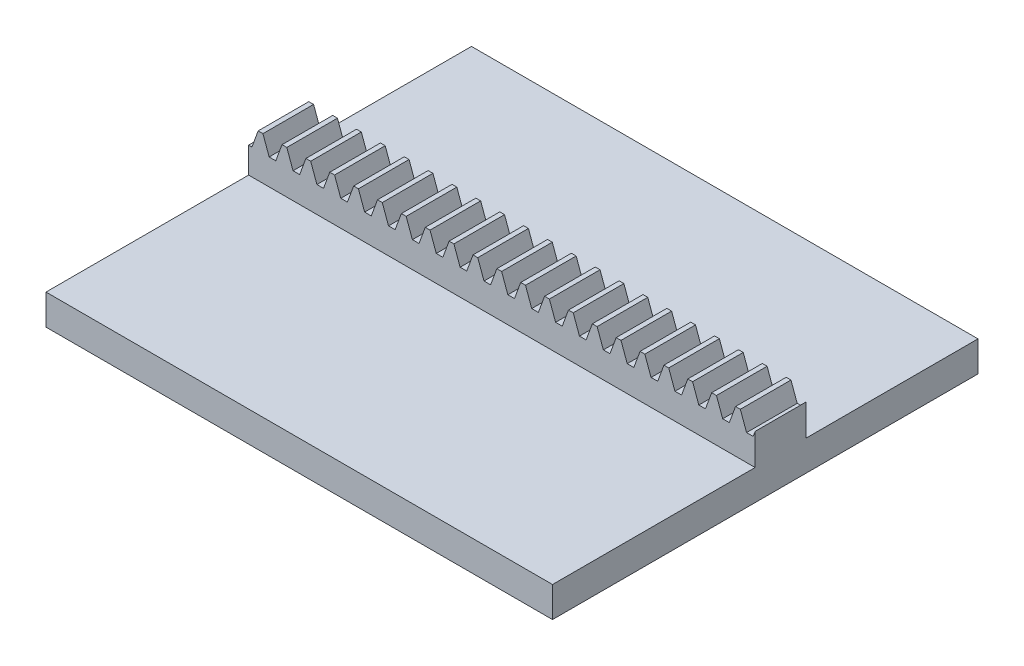
SolidWorks part; units mm, degrees
extrude "Blank" add sketch "BlankSke" against normal blind 10
sketch "BlankSke" plane through (0, 0, 0) normal (0, 0, 1) x (1, 0, 0)
  line L1 (0, 0) -> (100, 0)
  line L2 (0, 0) -> (0, 11.5)
  line L3 (0, 11.5) -> (100, 11.5)
  line L4 (100, 0) -> (100, 11.5)
  dimension "Length" = 100
  dimension "Blank_height" = 11.5
ref_plane "Plane1" through (0, 0, 0) normal (0, 0, 1) x (1, 0, 0)
ref_plane "Plane2" through (0, 0, 0) normal (0, 1, 0) x (1, 0, 0)
ref_plane "Plane3" through (0, 0, 0) normal (1, 0, 0) x (0, 0, -1)
other "Configuration Table"
sketch "HoldingSke" plane through (0, 0, 0) normal (0, 1, 0) x (1, 0, 0)
  line L0 (0, 0) -> (0.0928, 0.6602)
  line L1 (-15, 0) -> (100, 0) construction
  line L2 (0, 0) -> (-2.1039, 2.3779)
  line L3 (0, 0) -> (-11.863, 4.5341)
  line L4 (0, 0) -> (7.9495, 3.3743)
  line L5 (0, 0) -> (-23.7986, -8.8762)
  line L6 (0, 0) -> (-10.5278, -7.1032)
  line L9 (-71.009, 38.7566) -> (22.9603, 72.9586)
  line L10 (-76.2, 3.8779) -> (-66.2, 3.8779)
  line L11 (0, 0) -> (-10, 0)
  line L12 (-76.2, 101.6) -> (-76.147, 101.6)
  line L13 (24.9733, 27.94) -> (52.9518, 28.4284)
  line L14 (24.9733, 27.94) -> (24.9743, 27.94)
  line L15 (24.9733, 27.94) -> (100.4006, 29.5858)
  circle A0 centre (0, 0) radius 19.05
  circle A1 centre (0, 0) radius 5
  circle A2 centre (0, 0) radius 12.7
  dimension "MPH" = 10
  dimension "Diameter" = 38.1
  dimension "Num_teeth" = 23
  dimension "Pitch" = 0.6667
  dimension "Show_teeth" = 998
  dimension "Thickness" = 12.7
  dimension "Ap" = 20
  dimension "Pitch_height" = 10
  dimension "Width" = 10
  dimension "Backlash" = 0.053
  dimension "Addendum_fac" = 1
  dimension "Dedendum_fac" = 1.25
  dimension "Clearance_fac" = 0.25
  dimension "Dedendum_add" = 0.001
  dimension "Length" = 100
  dimension "Module" = 1.5
sketch "TooCutSkeIll" plane through (0, 0, 0) normal (0, 0, 1) x (1, 0, 0)
  line L0 (-1.8687, 11.4605) -> (-0.7447, 8.3724)
  line L1 (-0.3914, 8.125) -> (0.3914, 8.125)
  line L2 (0.7447, 8.3724) -> (1.8687, 11.4605)
  line L3 (100, 11.5) -> (0, 11.5) construction
  line L4 (0, 0) -> (0, 64.897) construction
  line L5 (-13.208, 10) -> (12.954, 10) construction
  line L6 (0, 0) -> (100, 0) construction
  line L7 (1.3371, 10) -> (1.3371, 48.7463) construction
  line L8 (-1.3371, 10) -> (-1.3371, 48.7463) construction
  line L9 (1.9251, 11.5) -> (1.9251, 11.5254)
  line L10 (-1.9251, 11.5) -> (-1.9251, 11.5254)
  line L11 (-1.9251, 11.5254) -> (1.9251, 11.5254)
  arc A0 (0.3914, 8.125) -> (0.7447, 8.3724) centre (0.3914, 8.501) ccw
  arc A1 (-0.7447, 8.3724) -> (-0.3914, 8.125) centre (-0.3914, 8.501) ccw
  arc A2 (1.9251, 11.5) -> (1.8687, 11.4605) centre (1.9251, 11.44) ccw
  arc A3 (-1.8687, 11.4605) -> (-1.9251, 11.5) centre (-1.9251, 11.44) ccw
  dimension "Pitch_height" = 10
  dimension "Addendum_plus" = 1.5254
  dimension "Pressure_angle" = 20
  dimension "Gap_width" = 2.6742
  dimension "Dedendum" = 1.875
extrude "ToothCutIll" [suppressed] cut sketch "TooCutSkeIll" against normal through all
sketch "TooCutSkeSim" plane through (0, 0, 0) normal (0, 0, 1) x (1, 0, 0)
  line L0 (0.6547, 8.125) -> (-0.6547, 8.125)
  line L1 (1.8923, 11.5254) -> (0.6547, 8.125)
  line L2 (0, 17.4625) -> (0, 53.467) construction
  line L3 (1.8923, 11.5254) -> (-1.8923, 11.5254)
  line L6 (-1.8923, 11.5254) -> (-0.6547, 8.125)
  line L9 (-1.3371, 10) -> (1.3371, 10) construction
  line L10 (0, 0) -> (100, 0) construction
  line L11 (1.3371, 10) -> (1.3371, 53.467) construction
  line L12 (-1.3371, 10) -> (-1.3371, 53.467) construction
  dimension "Pitch_height" = 10
  dimension "Addendum_plus" = 1.5254
  dimension "Pressure_angle" = 20
  dimension "Gap_width" = 2.6742
  dimension "Dedendum" = 1.875
extrude "ToothCutSim" cut sketch "TooCutSkeSim" against normal through all
pattern_linear "TeethCuts" count 22 spacing 4.7124 along (1, 0, 0) of "ToothCutIll", "ToothCutSim"
sketch "Sketch1" plane through (0, 0, 0) normal (0, 0, 1) x (1, 0, 0)
  line L4 (0, 8.125) -> (0, 0) construction
  line L5 (0, 3.044) -> (0, 0)
sketch "Sketch2" plane through (100, 0, 0) normal (1, 0, 0) x (0, 0, -1)
  line L25 (44.0001, 0) -> (44.0001, 3)
  line L26 (-40, 0) -> (44.0001, 0)
  line L27 (-40, 0) -> (-40, -3)
  line L28 (-40, -3) -> (44.0001, -3)
  line L29 (44.0001, 0) -> (44.0001, -3)
  line L30 (44.0001, 3) -> (10, 3)
  line L31 (10, 3) -> (10, 0)
  line L32 (10, 0) -> (44.0001, 0)
  line L33 (-40, 0) -> (0, 0)
  line L34 (0, 0) -> (0, 3)
  line L35 (0, 3) -> (-40, 3)
  line L36 (-40, 3) -> (-40, 0)
  line L37 (0, 0) -> (10, 0)
  line M13 (0, 9.1833) -> (0, 0)
  line M14 (0, 0) -> (10, 0)
  line M15 (10, 0) -> (10, 9.1833)
extrude "Boss-Extrude1" add sketch "Sketch2" against normal blind 100 contours L35 L36 L26 M13 | L25 L30 L26 M15 | L29 L26 L27 L28 M14
equation "' \"Module@HoldingSke\" = 6.35"
equation "' \"Num_teeth@HoldingSke\" = 12"
equation "' \"Ap@HoldingSke\" =  20"
equation "' \"Ap@HoldingSke\" = 20"
equation "' \"Width@HoldingSke\" = 0.25 * 25.4"
equation "' \"Show_teeth@HoldingSke\" = 500"
equation "' \"Backlash@HoldingSke\" = 0.009 * 25.4"
equation "' \"Addendum_fac@HoldingSke\" = 1.0"
equation "' \"Dedendum_fac@HoldingSke\" = 1.25"
equation "' \"Dedendum_add@HoldingSke\" = 0.00005 * 25.4"
equation "' \"Clearance_fac@HoldingSke\" = 0.25"
equation "' \"Pitch_height@HoldingSke\" = 1 * 25.4"
equation "' \"Length@HoldingSke\" = 4.71 * 25.4"
equation "\"Pitch@HoldingSke\" = 1 / \"Module@HoldingSke\""
equation "\"MPH@HoldingSke\" = \"Dedendum_fac@HoldingSke\" / \"Pitch@HoldingSke\" + 2 * \"Dedendum_add@HoldingSke\" + 0.002 * 25.4"
equation "\"MPH@HoldingSke\" = ((sgn( \"MPH@HoldingSke\" - \"Pitch_height@HoldingSke\")+1)*( \"MPH@HoldingSke\" - \"Pitch_height@HoldingSke\"))/2 + \"Pitch_height@HoldingSke\""
equation "\"Blank_height@BlankSke\" = \"Pitch_height@HoldingSke\" + \"Addendum_fac@HoldingSke\"  / \"Pitch@HoldingSke\" "
equation "\"Length@BlankSke\" =  \"Length@HoldingSke\""
equation "\"Face_width@Blank\" = \"Width@HoldingSke\""
equation "\"Pressure_angle@TooCutSkeIll\" = \"Ap@HoldingSke\""
equation "\"Addendum_plus@TooCutSkeIll\" =  \"Addendum_fac@HoldingSke\"  / \"Pitch@HoldingSke\" + 0.001 *25.4"
equation "\"Dedendum@TooCutSkeIll\" = \"Dedendum_fac@HoldingSke\"  / \"Pitch@HoldingSke\""
equation "\"Pitch_height@TooCutSkeIll\" =  \"MPH@HoldingSke\""
equation "\"Gap_width@TooCutSkeIll\" = 3.14159265 / 2 / \"Pitch@HoldingSke\" + 6 * \"Backlash@HoldingSke\""
equation "\"Pressure_angle@TooCutSkeSim\" = \"Ap@HoldingSke\""
equation "\"Addendum_plus@TooCutSkeSim\" =  \"Addendum_fac@HoldingSke\"  / \"Pitch@HoldingSke\" + 0.001 * 25.4"
equation "\"Dedendum@TooCutSkeSim\" = \"Dedendum_fac@HoldingSke\"  / \"Pitch@HoldingSke\""
equation "\"Pitch_height@TooCutSkeSim\" =  \"MPH@HoldingSke\""
equation "\"Gap_width@TooCutSkeSim\" = 3.14159265 / 2 / \"Pitch@HoldingSke\" + 6 * \"Backlash@HoldingSke\""
equation "\"Root_fillet@TooCutSkeIll\" = \"Clearance_fac@HoldingSke\" / \"Pitch@HoldingSke\" + \"Dedendum_add@HoldingSke\""
equation "\"Break_rad@TooCutSkeIll\" = 0.02 / \"Pitch@HoldingSke\" * 2"
equation "\"Linear_pitch@TeethCuts\" = 3.14159265 / \"Pitch@HoldingSke\""
equation "\"Num_teeth@HoldingSke\" = int( ( \"Length@HoldingSke\" + 0 ) / (3.14159265 / \"Pitch@HoldingSke\")) + 0.9999  + 1"
equation " \"Num_teeth@TeethCuts\" = int( \"Show_teeth@HoldingSke\" ) + 1"
equation " \"Num_teeth@TeethCuts\" = ((sgn( \"Num_teeth@TeethCuts\" - \"Num_teeth@HoldingSke\" )-1)*( \"Num_teeth@TeethCuts\" - \"Num_teeth@HoldingSke\" ))/-2+ \"Num_teeth@HoldingSke\""
equation " \"Num_teeth@TeethCuts\" = ((sgn( \"Num_teeth@TeethCuts\" - 2.0)+1)*( \"Num_teeth@TeethCuts\" - 2.0))/2 +2.0"
